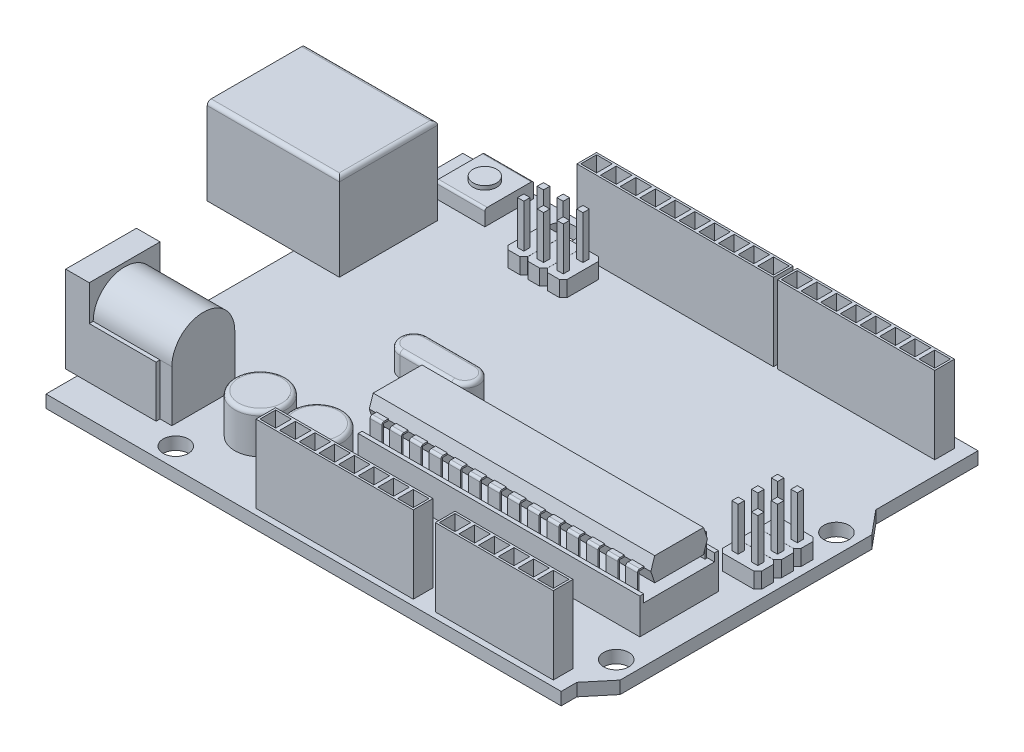
SolidWorks part; units mm, degrees
material "ABS"
ref_plane "정면" through (0, 0, 0) normal (0, 0, 1) x (1, 0, 0)
ref_plane "윗면" through (0, 0, 0) normal (0, 1, 0) x (1, 0, 0)
ref_plane "우측면" through (0, 0, 0) normal (1, 0, 0) x (0, 0, -1)
sketch "스케치1" plane through (0, 0, 0) normal (0, 1, 0) x (1, 0, 0)
  line L0 (0, 0) -> (0, 53)
  line L1 (0, 53) -> (65.5, 53)
  line L2 (65.5, 53) -> (65.5, 40)
  line L3 (65.5, 40) -> (68, 37)
  line L4 (68, 37) -> (68, 5)
  line L5 (68, 5) -> (65.5, 2)
  line L6 (65.5, 2) -> (65.5, 0)
  line L7 (65.5, 0) -> (0, 0)
  circle A0 centre (15, 50.5) radius 1.6
  circle A1 centre (65.5, 35) radius 1.6
  circle A2 centre (65.5, 7) radius 1.6
  circle A3 centre (14, 2.5) radius 1.6
  dimension "D1" = 3.2
  dimension "D2" = 40
  dimension "D3" = 15
  dimension "D4" = 50.5
  dimension "D5" = 53
  dimension "D6" = 37
  dimension "D7" = 68
  dimension "D8" = 2
  dimension "D9" = 65.5
  dimension "D10" = 5
  dimension "D11" = 7
  dimension "D12" = 35
  dimension "D13" = 14
  dimension "D14" = 2.5
extrude "보스-돌출1" add sketch "스케치1" along normal blind 1.6
sketch "스케치2" plane through (0, 1.6, 0) normal (0, 1, 0) x (1, 0, 0)
  line L0 (0, 53) -> (0, 0) construction
  line L1 (18.25, 51.75) -> (43.25, 51.75)
  line L2 (18.25, 51.75) -> (18.25, 49.25)
  line L3 (18.25, 49.25) -> (43.25, 49.25)
  line L4 (43.25, 51.75) -> (43.25, 49.25)
  line L5 (43.75, 51.75) -> (63.75, 51.75)
  line L6 (43.75, 51.75) -> (43.75, 49.25)
  line L7 (43.75, 49.25) -> (63.75, 49.25)
  line L8 (63.75, 51.75) -> (63.75, 49.25)
  line L9 (43, 51.5) -> (41, 51.5)
  line L10 (43, 51.5) -> (43, 49.5)
  line L11 (43, 49.5) -> (41, 49.5)
  line L12 (41, 51.5) -> (41, 49.5)
  line L13 (43, 51.5) -> (41, 49.5) construction
  line L14 (43, 49.5) -> (41, 51.5) construction
  line L15 (63.5, 49.5) -> (61.5, 49.5)
  line L16 (63.5, 49.5) -> (63.5, 51.5)
  line L17 (63.5, 51.5) -> (61.5, 51.5)
  line L18 (61.5, 49.5) -> (61.5, 51.5)
  line L19 (63.5, 49.5) -> (61.5, 51.5) construction
  line L20 (63.5, 51.5) -> (61.5, 49.5) construction
  line L21 (0, 0) -> (65.5, 0) construction
  line L22 (63.75, 50.5) -> (43.75, 50.5) construction
  line L23 (61, 49.5) -> (61, 51.5)
  line L24 (61, 49.5) -> (59, 49.5)
  line L25 (59, 49.5) -> (59, 51.5)
  line L26 (61, 51.5) -> (59, 51.5)
  line L27 (58.5, 49.5) -> (58.5, 51.5)
  line L28 (58.5, 49.5) -> (56.5, 49.5)
  line L29 (56.5, 49.5) -> (56.5, 51.5)
  line L30 (58.5, 51.5) -> (56.5, 51.5)
  line L31 (56, 49.5) -> (56, 51.5)
  line L32 (56, 49.5) -> (54, 49.5)
  line L33 (54, 49.5) -> (54, 51.5)
  line L34 (56, 51.5) -> (54, 51.5)
  line L35 (53.5, 49.5) -> (53.5, 51.5)
  line L36 (53.5, 49.5) -> (51.5, 49.5)
  line L37 (51.5, 49.5) -> (51.5, 51.5)
  line L38 (53.5, 51.5) -> (51.5, 51.5)
  line L39 (51, 49.5) -> (51, 51.5)
  line L40 (51, 49.5) -> (49, 49.5)
  line L41 (49, 49.5) -> (49, 51.5)
  line L42 (51, 51.5) -> (49, 51.5)
  line L43 (48.5, 49.5) -> (48.5, 51.5)
  line L44 (48.5, 49.5) -> (46.5, 49.5)
  line L45 (46.5, 49.5) -> (46.5, 51.5)
  line L46 (48.5, 51.5) -> (46.5, 51.5)
  line L47 (46, 49.5) -> (46, 51.5)
  line L48 (46, 49.5) -> (44, 49.5)
  line L49 (44, 49.5) -> (44, 51.5)
  line L50 (46, 51.5) -> (44, 51.5)
  line L51 (40.5, 51.5) -> (40.5, 49.5)
  line L52 (40.5, 51.5) -> (38.5, 51.5)
  line L53 (38.5, 51.5) -> (38.5, 49.5)
  line L54 (40.5, 49.5) -> (38.5, 49.5)
  line L55 (38, 51.5) -> (38, 49.5)
  line L56 (38, 51.5) -> (36, 51.5)
  line L57 (36, 51.5) -> (36, 49.5)
  line L58 (38, 49.5) -> (36, 49.5)
  line L59 (35.5, 51.5) -> (35.5, 49.5)
  line L60 (35.5, 51.5) -> (33.5, 51.5)
  line L61 (33.5, 51.5) -> (33.5, 49.5)
  line L62 (35.5, 49.5) -> (33.5, 49.5)
  line L63 (33, 51.5) -> (33, 49.5)
  line L64 (33, 51.5) -> (31, 51.5)
  line L65 (31, 51.5) -> (31, 49.5)
  line L66 (33, 49.5) -> (31, 49.5)
  line L67 (30.5, 51.5) -> (30.5, 49.5)
  line L68 (30.5, 51.5) -> (28.5, 51.5)
  line L69 (28.5, 51.5) -> (28.5, 49.5)
  line L70 (30.5, 49.5) -> (28.5, 49.5)
  line L71 (28, 51.5) -> (28, 49.5)
  line L72 (28, 51.5) -> (26, 51.5)
  line L73 (26, 51.5) -> (26, 49.5)
  line L74 (28, 49.5) -> (26, 49.5)
  line L75 (25.5, 51.5) -> (25.5, 49.5)
  line L76 (25.5, 51.5) -> (23.5, 51.5)
  line L77 (23.5, 51.5) -> (23.5, 49.5)
  line L78 (25.5, 49.5) -> (23.5, 49.5)
  line L79 (23, 51.5) -> (23, 49.5)
  line L80 (23, 51.5) -> (21, 51.5)
  line L81 (21, 51.5) -> (21, 49.5)
  line L82 (23, 49.5) -> (21, 49.5)
  line L83 (20.5, 51.5) -> (20.5, 49.5)
  line L84 (20.5, 51.5) -> (18.5, 51.5)
  line L85 (18.5, 51.5) -> (18.5, 49.5)
  line L86 (20.5, 49.5) -> (18.5, 49.5)
  line L87 (48.75, 3.25) -> (63.75, 3.25)
  line L88 (48.75, 3.25) -> (48.75, 0.75)
  line L89 (48.75, 0.75) -> (63.75, 0.75)
  line L90 (63.75, 3.25) -> (63.75, 0.75)
  line L91 (63.5, 1) -> (61.5, 1)
  line L92 (63.5, 1) -> (63.5, 3)
  line L93 (63.5, 3) -> (61.5, 3)
  line L94 (61.5, 1) -> (61.5, 3)
  line L95 (63.5, 1) -> (61.5, 3) construction
  line L96 (63.5, 3) -> (61.5, 1) construction
  line L97 (63.75, 2) -> (48.75, 2) construction
  line L126 (61, 1) -> (59, 1)
  line L127 (59, 1) -> (59, 3)
  line L128 (61, 3) -> (59, 3)
  line L129 (61, 1) -> (61, 3)
  line L130 (58.5, 1) -> (56.5, 1)
  line L131 (56.5, 1) -> (56.5, 3)
  line L132 (58.5, 3) -> (56.5, 3)
  line L133 (58.5, 1) -> (58.5, 3)
  line L134 (56, 1) -> (54, 1)
  line L135 (54, 1) -> (54, 3)
  line L136 (56, 3) -> (54, 3)
  line L137 (56, 1) -> (56, 3)
  line L138 (53.5, 1) -> (51.5, 1)
  line L139 (51.5, 1) -> (51.5, 3)
  line L140 (53.5, 3) -> (51.5, 3)
  line L141 (53.5, 1) -> (53.5, 3)
  line L142 (51, 1) -> (49, 1)
  line L143 (49, 1) -> (49, 3)
  line L144 (51, 3) -> (49, 3)
  line L145 (51, 1) -> (51, 3)
  line L146 (25.95, 3.25) -> (45.95, 3.25)
  line L147 (25.95, 3.25) -> (25.95, 0.75)
  line L148 (25.95, 0.75) -> (45.95, 0.75)
  line L149 (45.95, 3.25) -> (45.95, 0.75)
  line L150 (45.7, 1) -> (43.7, 1)
  line L151 (45.7, 1) -> (45.7, 3)
  line L152 (45.7, 3) -> (43.7, 3)
  line L153 (43.7, 1) -> (43.7, 3)
  line L154 (45.7, 1) -> (43.7, 3) construction
  line L155 (45.7, 3) -> (43.7, 1) construction
  line L156 (25.95, 2) -> (45.95, 2) construction
  line L185 (43.2, 1) -> (41.2, 1)
  line L186 (41.2, 1) -> (41.2, 3)
  line L187 (43.2, 3) -> (41.2, 3)
  line L188 (43.2, 1) -> (43.2, 3)
  line L189 (40.7, 1) -> (38.7, 1)
  line L190 (38.7, 1) -> (38.7, 3)
  line L191 (40.7, 3) -> (38.7, 3)
  line L192 (40.7, 1) -> (40.7, 3)
  line L193 (38.2, 1) -> (36.2, 1)
  line L194 (36.2, 1) -> (36.2, 3)
  line L195 (38.2, 3) -> (36.2, 3)
  line L196 (38.2, 1) -> (38.2, 3)
  line L197 (35.7, 1) -> (33.7, 1)
  line L198 (33.7, 1) -> (33.7, 3)
  line L199 (35.7, 3) -> (33.7, 3)
  line L200 (35.7, 1) -> (35.7, 3)
  line L201 (33.2, 1) -> (31.2, 1)
  line L202 (31.2, 1) -> (31.2, 3)
  line L203 (33.2, 3) -> (31.2, 3)
  line L204 (33.2, 1) -> (33.2, 3)
  line L205 (30.7, 1) -> (28.7, 1)
  line L206 (28.7, 1) -> (28.7, 3)
  line L207 (30.7, 3) -> (28.7, 3)
  line L208 (30.7, 1) -> (30.7, 3)
  line L209 (28.2, 1) -> (26.2, 1)
  line L210 (26.2, 1) -> (26.2, 3)
  line L211 (28.2, 3) -> (26.2, 3)
  line L212 (28.2, 1) -> (28.2, 3)
  point P8 (42, 50.5)
  point P13 (62.5, 50.5)
  point P93 (62.5, 2)
  point P123 (44.7, 2)
  dimension "D1" = 42
  dimension "D2" = 62.5
  dimension "D3" = 2.5
  dimension "D4" = 44.7
  dimension "D6" = 2.5
  dimension "D7" = 2
  dimension "D8" = 0.25
  dimension "D9" = 0.25
  dimension "D10" = 0.25
  dimension "D12" = 0.25
  dimension "D13" = 2.5
  dimension "D14" = 2.5
  dimension "D15" = 62.5
  dimension "D16" = 2
  dimension "D17" = 0.25
  dimension "D18" = 2
  dimension "D20" = 2.5
  dimension "D21" = 0.25
  dimension "D22" = 2.5
  dimension "D23" = 8
  dimension "D24" = 2
  dimension "D25" = 0.25
  dimension "D26" = 2.5
  dimension "D27" = 0.25
  dimension "D5" = 8
  dimension "D11" = 10
  dimension "D19" = 6
extrude "보스-돌출2" add sketch "스케치2" along normal blind 9.84
sketch "스케치4" plane through (0, 1.6, 0) normal (0, 1, 0) x (1, 0, 0)
  line L0 (0, 53) -> (0, 0) construction
  line L1 (-11, 44) -> (5.8, 44)
  line L2 (-11, 44) -> (-11, 31.5)
  line L3 (-11, 31.5) -> (5.8, 31.5)
  line L4 (5.8, 44) -> (5.8, 31.5)
  line L5 (65.5, 53) -> (0, 53) construction
  dimension "D1" = 16.8
  dimension "D2" = 12.5
  dimension "D3" = 11
  dimension "D4" = 9
extrude "보스-돌출3" add sketch "스케치4" along normal blind 11
sketch "스케치5" plane through (-11, 0, 0) normal (-1, 0, 0) x (0, 0, 1)
  line L0 (-42.5, 9) -> (-42.5, 3.1)
  line L1 (-42.5, 3.1) -> (-33, 3.1)
  line L2 (-33, 3.1) -> (-33, 9)
  line L3 (-33, 9) -> (-35.1, 11.1)
  line L4 (-35.1, 11.1) -> (-40.4, 11.1)
  line L5 (-40.4, 11.1) -> (-42.5, 9)
  line L6 (-37.75, 11.1) -> (-37.75, 3.1) construction
  line L7 (-40.4, 9) -> (-35.1, 9)
  line L8 (-40.4, 9) -> (-40.4, 6)
  line L9 (-40.4, 6) -> (-35.1, 6)
  line L10 (-35.1, 9) -> (-35.1, 6)
  line L11 (-44, 12.6) -> (-31.5, 12.6) construction
  line L12 (-44, 12.6) -> (-44, 1.6) construction
  line L13 (-44, 1.6) -> (-31.5, 1.6) construction
  point P12 (-37.75, 12.6)
  dimension "D1" = 1.5
  dimension "D2" = 1.5
  dimension "D3" = 135
  dimension "D4" = 1.5
  dimension "D5" = 3
  dimension "D6" = 5.3
extrude "컷-돌출1" cut sketch "스케치5" against normal blind 10
sketch "스케치7" plane through (0, 0, 0) normal (-1, 0, 0) x (0, 0, 1)
  line L0 (-31.5, 1.6) -> (0, 1.6) construction
  line L1 (-13, 12.6) -> (-4, 12.6)
  line L2 (-13, 12.6) -> (-13, 1.6)
  line L3 (-13, 1.6) -> (-4, 1.6)
  line L4 (-4, 12.6) -> (-4, 1.6)
  line L5 (-8.5, 12.6) -> (-8.5, 8.1) construction
  line L6 (-8.5, 8.1) -> (-4, 8.1) construction
  line L7 (0, 1.6) -> (0, 0) construction
  circle A0 centre (-8.5, 8.1) radius 3.25
  dimension "D3" = 6.5
  dimension "D1" = 11
  dimension "D2" = 9
  dimension "D4" = 13
extrude "보스-돌출4" add sketch "스케치7" along normal blind 1.5 and the other way blind 10
sketch "스케치8" plane through (10, 0, 0) normal (1, 0, 0) x (0, 0, -1)
  line L0 (4.5, 8.1) -> (4, 8.1)
  line L1 (4, 1.6) -> (4, 12.6) construction
  line L2 (4, 8.1) -> (4, 12.6)
  line L3 (4, 12.6) -> (13, 12.6)
  line L4 (4, 12.6) -> (13, 12.6) construction
  line L5 (13, 12.6) -> (13, 8.1)
  line L6 (13, 12.6) -> (13, 1.6) construction
  line L7 (13, 8.1) -> (12.5, 8.1)
  arc A0 (12.5, 8.1) -> (4.5, 8.1) centre (8.5, 8.1) ccw
  dimension "D1" = 8
extrude "컷-돌출2" cut sketch "스케치8" against normal blind 8.5
sketch "스케치9" plane through (10, 0, 0) normal (1, 0, 0) x (0, 0, -1)
  line L0 (4.5, 8.1) -> (4.5, 1.6)
  line L1 (2, 1.6) -> (5, 1.6) construction
  line L2 (4.5, 1.6) -> (12.5, 1.6)
  line L3 (13, 1.6) -> (4, 1.6) construction
  line L4 (12.5, 1.6) -> (12.5, 8.1)
  arc A0 (12.5, 8.1) -> (4.5, 8.1) centre (8.5, 8.1) ccw construction
  arc A1 (12.5, 8.1) -> (4.5, 8.1) centre (8.5, 8.1) ccw
extrude "보스-돌출5" add sketch "스케치9" along normal blind 1.5
sketch "스케치10" plane through (0, 1.6, 0) normal (0, 1, 0) x (1, 0, 0)
  line L0 (0, 0) -> (65.5, 0) construction
  line L1 (11.5, 4.5) -> (11.5, 12.5) construction
  circle A0 centre (18.25, 9) radius 3.25
  circle A1 centre (25.45, 9) radius 3.25
  point P7 (15, 9)
  dimension "D1" = 6.5
  dimension "D2" = 9
  dimension "D3" = 7.2
  dimension "D4" = 3.5
extrude "보스-돌출6" add sketch "스케치10" along normal blind 5
fillet "필렛1" radius 0.5 2 edges at (25.45, 6.6, -5.75) (18.25, 6.6, -5.75)
fillet "필렛2" radius 0.5 3 edges at (5.8, 12.6, -37.75) (-2.6, 12.6, -44) (-2.6, 12.6, -31.5)
sketch "스케치11" plane through (10, 0, 0) normal (-1, 0, 0) x (0, 0, 1)
  circle A0 centre (-8.5, 8.1) radius 1
  dimension "D1" = 2
extrude "보스-돌출7" add sketch "스케치11" along normal blind 10
fillet "필렛3" radius 1 1 edges at (0, 8.1, -7.5)
sketch "스케치12" plane through (0, 1.6, 0) normal (0, 1, 0) x (1, 0, 0)
  line L0 (5.8, 31.5) -> (-11, 31.5) construction
  line L1 (20.75, 27.75) -> (27.25, 27.75)
  line L3 (20.75, 24.25) -> (27.25, 24.25)
  line L5 (0, 31.5) -> (0, 13) construction
  arc A0 (20.75, 27.75) -> (20.75, 24.25) centre (20.75, 26) ccw
  arc A1 (27.25, 24.25) -> (27.25, 27.75) centre (27.25, 26) ccw
  point P1 (29, 26)
  point P3 (19, 26)
  dimension "D1" = 3.5
  dimension "D2" = 10
  dimension "D3" = 5.5
  dimension "D4" = 19
extrude "보스-돌출8" add sketch "스케치12" along normal blind 3
fillet "필렛4" radius 0.5 4 edges at (24, 4.6, -27.75) (29, 4.6, -26) (24, 4.6, -24.25) (19, 4.6, -26)
sketch "스케치13" plane through (0, 1.6, 0) normal (0, 1, 0) x (1, 0, 0)
  line L0 (0, 0) -> (65.5, 0) construction
  line L1 (28.7, 21) -> (64.5, 21)
  line L2 (28.7, 21) -> (28.7, 11)
  line L3 (28.7, 11) -> (64.5, 11)
  line L4 (64.5, 21) -> (64.5, 11)
  line L5 (68, 5) -> (68, 37) construction
  point P5 (64.5, 16)
  dimension "D1" = 10
  dimension "D2" = 35.8
  dimension "D3" = 16
  dimension "D4" = 3.5
extrude "보스-돌출9" add sketch "스케치13" along normal blind 8
sketch "스케치14" plane through (64.5, 0, 0) normal (1, 0, 0) x (0, 0, -1)
  line L0 (12.9, 9.6) -> (12.4, 8.1)
  line L1 (11, 9.6) -> (21, 9.6) construction
  line L2 (12.4, 8.1) -> (12.9, 6.6)
  line L3 (12.9, 9.6) -> (11, 9.6)
  line L4 (19.1, 9.6) -> (19.6, 8.1)
  line L5 (19.1, 9.6) -> (21, 9.6)
  line L6 (11, 9.6) -> (11, 1.6) construction
  line L7 (12.9, 6.6) -> (11, 6.6)
  line L8 (11, 6.6) -> (11, 9.6)
  line L9 (16, 9.6) -> (16, 1.6) construction
  line L10 (11, 1.6) -> (21, 1.6) construction
  line L11 (21, 6.6) -> (21, 9.6)
  line L12 (19.1, 6.6) -> (21, 6.6)
  line L13 (19.6, 8.1) -> (19.1, 6.6)
  dimension "D1" = 3
  dimension "D2" = 1.5
  dimension "D3" = 0.5
  dimension "D4" = 7.2
extrude "컷-돌출3" cut sketch "스케치14" against normal up to surface (35.8 mm away) up to face at (28.7, 5.6, -16)
sketch "스케치15" plane through (64.5, 0, 0) normal (1, 0, 0) x (0, 0, -1)
  line L0 (21, 6.6) -> (21, 1.6) construction
  line L1 (11, 6.6) -> (21, 6.6)
  line L2 (11, 6.6) -> (11, 5.1)
  line L3 (11, 5.1) -> (21, 5.1)
  line L4 (21, 6.6) -> (21, 5.1)
  dimension "D1" = 1.5
extrude "컷-돌출4" cut sketch "스케치15" against normal up to surface (35.8 mm away) up to face at (28.7, 6.5, -16)
sketch "스케치16" plane through (64.5, 0, 0) normal (1, 0, 0) x (0, 0, -1)
  line L1 (11, 5.1) -> (11.5, 5.1)
  line L2 (11, 5.1) -> (11, 6.1)
  line L3 (11, 6.1) -> (11.5, 6.1)
  line L4 (11.5, 5.1) -> (11.5, 6.1)
  line L5 (21, 5.1) -> (20.5, 5.1)
  line L6 (21, 5.1) -> (21, 6.1)
  line L7 (21, 6.1) -> (20.5, 6.1)
  line L8 (20.5, 5.1) -> (20.5, 6.1)
  dimension "D1" = 0.5
  dimension "D2" = 1
extrude "보스-돌출10" add sketch "스케치16" against normal up to surface (35.8 mm away) up to face at (28.7, 3.35, -16)
ref_plane "평면1" through (63.6, 0, 0) normal (1, 0, 0) x (0, 0, -1)
sketch "스케치17" plane through (63.6, 0, 0) normal (1, 0, 0) x (0, 0, -1)
  line L0 (12.4333, 8.2) -> (12.4333, 8)
  line L2 (12.4333, 8) -> (11.8, 8)
  line L3 (11.8, 8) -> (11.8, 5.1)
  line L4 (11.8, 5.1) -> (11.6, 5.1)
  line L5 (11.6, 5.1) -> (11.6, 8.2)
  line L6 (11.6, 8.2) -> (12.4333, 8.2)
  line L7 (16, 9.6) -> (16, 6.6) construction
  line L8 (12.9, 9.6) -> (19.1, 9.6) construction
  line L9 (19.1, 6.6) -> (12.9, 6.6) construction
  line L10 (20.4, 5.1) -> (20.4, 8.2)
  line L11 (20.2, 5.1) -> (20.4, 5.1)
  line L12 (20.2, 8) -> (20.2, 5.1)
  line L13 (19.5667, 8) -> (20.2, 8)
  line L14 (19.5667, 8.2) -> (19.5667, 8)
  line L15 (20.4, 8.2) -> (19.5667, 8.2)
  line L16 (12.4333, 8.1) -> (16, 8.1) construction
  line L17 (12.4, 8.1) -> (12.9, 9.6) construction
  line L18 (11.5, 5.1) -> (20.5, 5.1) construction
  line L19 (11.5, 5.1) -> (11.5, 6.1) construction
  dimension "D1" = 0.2
  dimension "D2" = 0.1
extrude "보스-돌출11" add sketch "스케치17" against normal blind 1.5
fillet "필렛5" radius 0.3 2 edges at (62.85, 8.2, -20.4) (62.85, 8.2, -11.6)
pattern_linear "선형 패턴2" count 14 spacing 2.5 along (-1, 0, 0) of "보스-돌출11", "필렛5"
sketch "스케치18" plane through (0, 1.6, 0) normal (0, 1, 0) x (1, 0, 0)
  line L0 (66.5, 26) -> (62.5, 26)
  line L1 (62.5, 26) -> (62, 25.5)
  line L2 (62, 25.5) -> (62, 24)
  line L3 (62, 24) -> (62.5, 23.5)
  line L4 (62.5, 23.5) -> (66.5, 23.5)
  line L5 (66.5, 23.5) -> (67, 24)
  line L6 (67, 24) -> (67, 25.5)
  line L7 (67, 25.5) -> (66.5, 26)
  line L9 (68, 5) -> (68, 37) construction
  dimension "D1" = 5
  dimension "D2" = 2.5
  dimension "D3" = 135
  dimension "D4" = 0.5
  dimension "D5" = 16.5
  dimension "D6" = 1
extrude "보스-돌출12" add sketch "스케치18" along normal blind 2
sketch "스케치19" plane through (0, 3.6, 0) normal (0, 1, 0) x (1, 0, 0)
  line L0 (62, 24.75) -> (67, 24.75) construction
  line L9 (62, 25.5) -> (62, 24) construction
  line L10 (67, 24) -> (67, 25.5) construction
  line L12 (63.65, 24.35) -> (62.85, 24.35)
  line L13 (63.65, 24.35) -> (63.65, 25.15)
  line L14 (63.65, 25.15) -> (62.85, 25.15)
  line L15 (62.85, 24.35) -> (62.85, 25.15)
  line L16 (63.65, 24.35) -> (62.85, 25.15) construction
  line L17 (63.65, 25.15) -> (62.85, 24.35) construction
  line L18 (66.15, 24.35) -> (65.35, 24.35)
  line L19 (66.15, 24.35) -> (66.15, 25.15)
  line L20 (66.15, 25.15) -> (65.35, 25.15)
  line L21 (65.35, 24.35) -> (65.35, 25.15)
  line L22 (66.15, 24.35) -> (65.35, 25.15) construction
  line L23 (66.15, 25.15) -> (65.35, 24.35) construction
  point P0 (63.25, 24.75)
  point P5 (65.75, 24.75)
  dimension "D1" = 0.8
  dimension "D2" = 1.25
  dimension "D3" = 1.25
extrude "보스-돌출13" add sketch "스케치19" along normal blind 5.5
pattern_linear "선형 패턴3" count 3 spacing 2.51 along (0, 0, -1) of "보스-돌출12", "보스-돌출13"
sketch "스케치20" plane through (0, 1.6, 0) normal (0, 1, 0) x (1, 0, 0)
  line L0 (15, 47.75) -> (15, 43.75)
  line L1 (15, 43.75) -> (15.5, 43.25)
  line L2 (15.5, 43.25) -> (17, 43.25)
  line L3 (17, 43.25) -> (17.5, 43.75)
  line L4 (17.5, 43.75) -> (17.5, 47.75)
  line L5 (17.5, 47.75) -> (17, 48.25)
  line L6 (17, 48.25) -> (15.5, 48.25)
  line L7 (15.5, 48.25) -> (15, 47.75)
  line L8 (43.25, 51.75) -> (18.25, 51.75) construction
  line L9 (0, 53) -> (0, 44) construction
  dimension "D1" = 5
  dimension "D2" = 2.5
  dimension "D3" = 135
  dimension "D4" = 0.5
  dimension "D5" = 8.5
  dimension "D6" = 15
extrude "보스-돌출14" add sketch "스케치20" along normal up to surface (2 mm away) up to face at (64.5, 3.6, -29.77)
sketch "스케치21" plane through (0, 3.6, 0) normal (0, 1, 0) x (1, 0, 0)
  line L0 (16.25, 48.25) -> (16.25, 43.25) construction
  line L1 (16.65, 46.6) -> (15.85, 46.6)
  line L2 (16.65, 46.6) -> (16.65, 47.4)
  line L3 (16.65, 47.4) -> (15.85, 47.4)
  line L4 (15.85, 46.6) -> (15.85, 47.4)
  line L5 (16.65, 46.6) -> (15.85, 47.4) construction
  line L6 (16.65, 47.4) -> (15.85, 46.6) construction
  line L7 (16.65, 44.1) -> (15.85, 44.1)
  line L8 (16.65, 44.1) -> (16.65, 44.9)
  line L9 (16.65, 44.9) -> (15.85, 44.9)
  line L10 (15.85, 44.1) -> (15.85, 44.9)
  line L11 (16.65, 44.1) -> (15.85, 44.9) construction
  line L12 (16.65, 44.9) -> (15.85, 44.1) construction
  line L13 (17, 48.25) -> (15.5, 48.25) construction
  line L14 (15.5, 43.25) -> (17, 43.25) construction
  point P0 (16.25, 47)
  point P5 (16.25, 44.5)
  dimension "D1" = 0.8
  dimension "D2" = 1.25
  dimension "D3" = 1.25
extrude "보스-돌출15" add sketch "스케치21" along normal up to surface (5.5 mm away) up to face at (63.25, 9.1, -29.77)
pattern_linear "선형 패턴4" count 3 spacing 2.51 along (1, 0, 0) of "보스-돌출14", "보스-돌출15"
sketch "스케치22" plane through (0, 1.6, 0) normal (0, 1, 0) x (1, 0, 0)
  line L0 (0, 53) -> (0, 44) construction
  line L1 (9.5, 46.3) -> (3.3, 46.3)
  line L2 (9.5, 46.3) -> (9.5, 52.5)
  line L3 (9.5, 52.5) -> (3.3, 52.5)
  line L4 (3.3, 46.3) -> (3.3, 52.5)
  line L5 (9.5, 46.3) -> (3.3, 52.5) construction
  line L6 (9.5, 52.5) -> (3.3, 46.3) construction
  line L7 (65.5, 53) -> (0, 53) construction
  point P0 (6.4, 49.4)
  dimension "D1" = 6.2
  dimension "D2" = 9.5
  dimension "D3" = 0.5
extrude "보스-돌출16" add sketch "스케치22" along normal blind 2
sketch "스케치23" plane through (0, 3.6, 0) normal (0, 1, 0) x (1, 0, 0)
  line L0 (6.4, 52.5) -> (6.4, 49.4) construction
  line L1 (9.5, 52.5) -> (3.3, 52.5) construction
  line L2 (6.4, 49.4) -> (9.5, 49.4) construction
  line L3 (9.5, 46.3) -> (9.5, 52.5) construction
  circle A0 centre (6.4, 49.4) radius 1.5
  dimension "D1" = 3
extrude "보스-돌출17" add sketch "스케치23" along normal blind 0.5
fillet "필렛6" radius 0.3 2 edges at (6.4, 3.6, -52.5) (6.4, 3.6, -46.3)
equation "\"16l8\"=20.3059"
